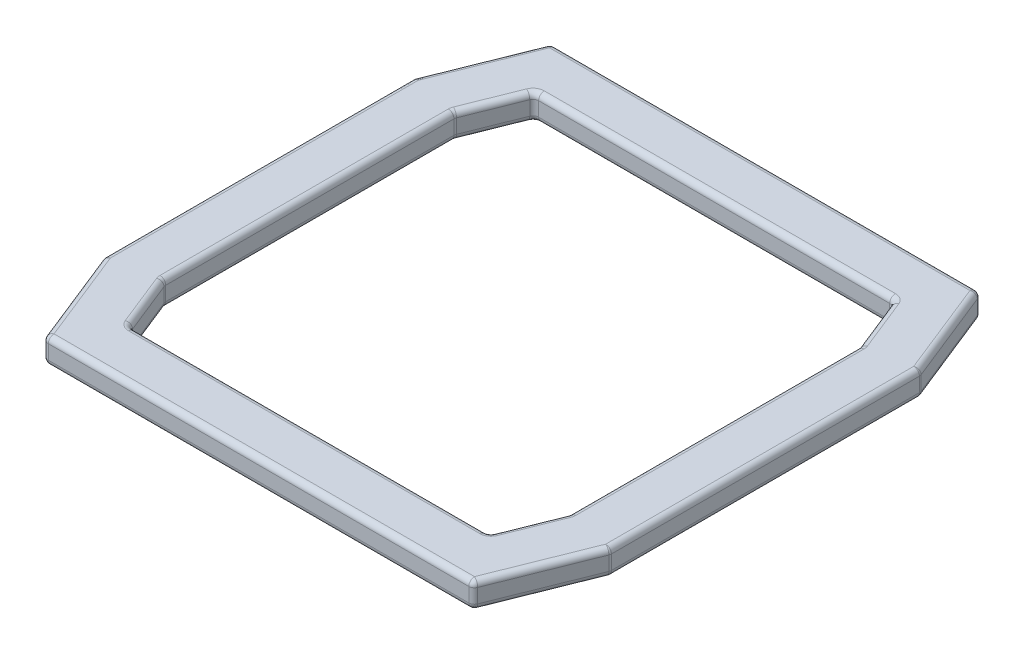
SolidWorks part; units mm, degrees
material "Copper"
ref_plane "Front Plane" through (0, 0, 0) normal (0, 0, 1) x (1, 0, 0)
ref_plane "Top Plane" through (0, 0, 0) normal (0, 1, 0) x (1, 0, 0)
ref_plane "Right Plane" through (0, 0, 0) normal (1, 0, 0) x (0, 0, -1)
sketch "Sketch1" plane through (0, 0, 0) normal (0, 1, 0) x (1, 0, 0)
  line L1 (-31.5, -35.5) -> (31.5, -35.5)
  line L2 (-35.5, -25.5) -> (-35.5, 25.5)
  line L4 (35.5, -25.5) -> (35.5, 25.5)
  line L5 (44.5, 0) -> (0, 0) construction
  line L6 (0, 0) -> (0, 44.5) construction
  line L7 (35.5, 25.5) -> (31.5, 35.5)
  line L8 (31.5, -35.5) -> (35.5, -25.5)
  line L9 (-35.5, -25.5) -> (-31.5, -35.5)
  line L10 (-31.5, 35.5) -> (-35.5, 25.5)
  line L11 (31.5, 35.5) -> (-31.5, 35.5)
  line L29 (-37.5933, -44.5) -> (37.5933, -44.5)
  line L30 (37.5933, -44.5) -> (44.5, -27.2332)
  line L31 (44.5, -27.2332) -> (44.5, 27.2332)
  line L32 (44.5, 27.2332) -> (37.5933, 44.5)
  line L33 (37.5933, 44.5) -> (-37.5933, 44.5)
  line L34 (-37.5933, 44.5) -> (-44.5, 27.2332)
  line L35 (-44.5, -27.2332) -> (-44.5, 27.2332)
  line L36 (-44.5, -27.2332) -> (-37.5933, -44.5)
  point P4 (0, 0)
  point P9 (0, 0)
  dimension "D1" = 71
  dimension "D4" = 10
  dimension "D5" = 4
  dimension "D8" = 4
  dimension "D9" = 10
  dimension "D7" = 4
  dimension "D3" = 10
  dimension "D10" = 10
  dimension "D11" = 4
  dimension "D12" = 71
  dimension "D6" = 9
extrude "Boss-Extrude1" add sketch "Sketch1" along normal mid plane 4.5
fillet "Fillet1" radius 1 48 edges at (31.5, 0, -35.5) (35.5, 0, -25.5) (-35.5, 0, -25.5) (-31.5, 0, -35.5) (-31.5, 0, 35.5) (-35.5, 0, 25.5) (35.5, 0, 25.5) (31.5, 0, 35.5) (37.5933, 0, 44.5) (44.5, 0, 27.2332) (-44.5, 0, 27.2332) (-37.5933, 0, 44.5) (-37.5933, 0, -44.5) (-44.5, 0, -27.2332) (44.5, 0, -27.2332) (37.5933, 0, -44.5) (35.5, -2.25, 0) (33.5, -2.25, 30.5) (0, -2.25, 35.5) (-33.5, -2.25, 30.5) (-35.5, -2.25, 0) (-33.5, -2.25, -30.5) (0, -2.25, -35.5) (33.5, -2.25, -30.5) (0, -2.25, 44.5) (41.0466, -2.25, 35.8666) (44.5, -2.25, 0) (41.0466, -2.25, -35.8666) (0, -2.25, -44.5) (-41.0466, -2.25, -35.8666) (-44.5, -2.25, 0) (-41.0466, -2.25, 35.8666) (-33.5, 2.25, -30.5) (-35.5, 2.25, 0) (-33.5, 2.25, 30.5) (0, 2.25, 35.5) (33.5, 2.25, 30.5) (35.5, 2.25, 0) (33.5, 2.25, -30.5) (0, 2.25, -35.5) (-44.5, 2.25, 0) (-41.0466, 2.25, -35.8666) (0, 2.25, -44.5) (41.0466, 2.25, -35.8666) (44.5, 2.25, 0) (41.0466, 2.25, 35.8666) (0, 2.25, 44.5) (-41.0466, 2.25, 35.8666)
